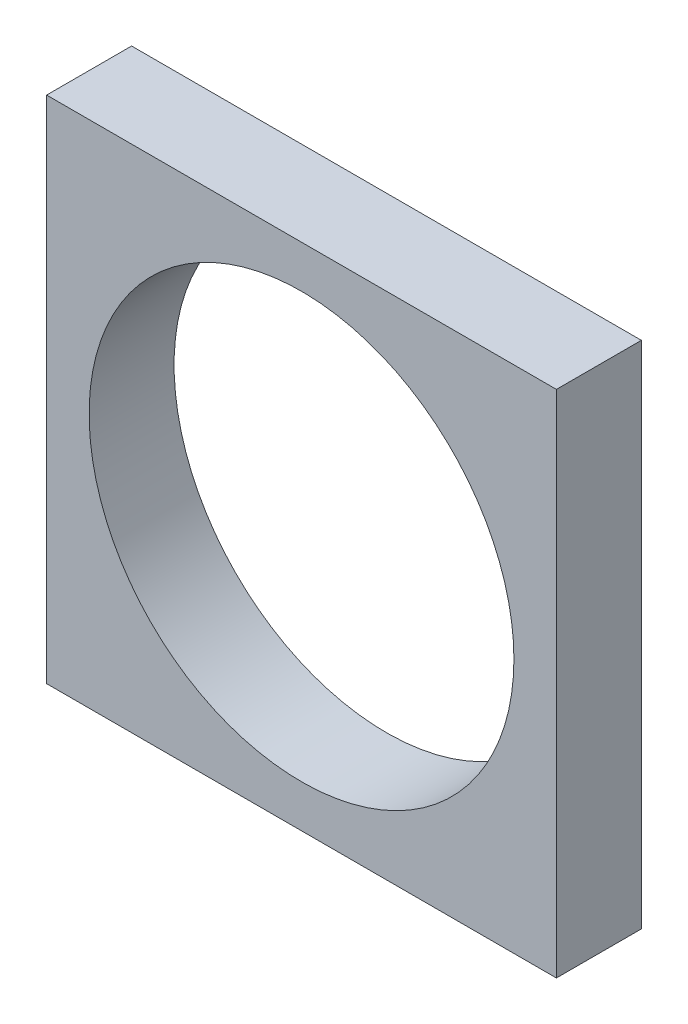
SolidWorks part; units mm, degrees
ref_plane "Piano frontale" through (0, 0, 0) normal (0, 0, 1) x (1, 0, 0)
ref_plane "Piano superiore" through (0, 0, 0) normal (0, 1, 0) x (1, 0, 0)
ref_plane "Piano destro" through (0, 0, 0) normal (1, 0, 0) x (0, 0, -1)
sketch "Schizzo1" plane through (0, 0, 0) normal (0, 0, 1) x (1, 0, 0)
  line L1 (-30, 30) -> (30, 30)
  line L2 (-30, 30) -> (-30, -30)
  line L3 (-30, -30) -> (30, -30)
  line L4 (30, 30) -> (30, -30)
  circle A0 centre (0, 0) radius 25
  dimension "D1" = 60
  dimension "D2" = 60
  dimension "D3" = 30
extrude "Estrusione-Estrusione2" add sketch "Schizzo1" along normal blind 10
